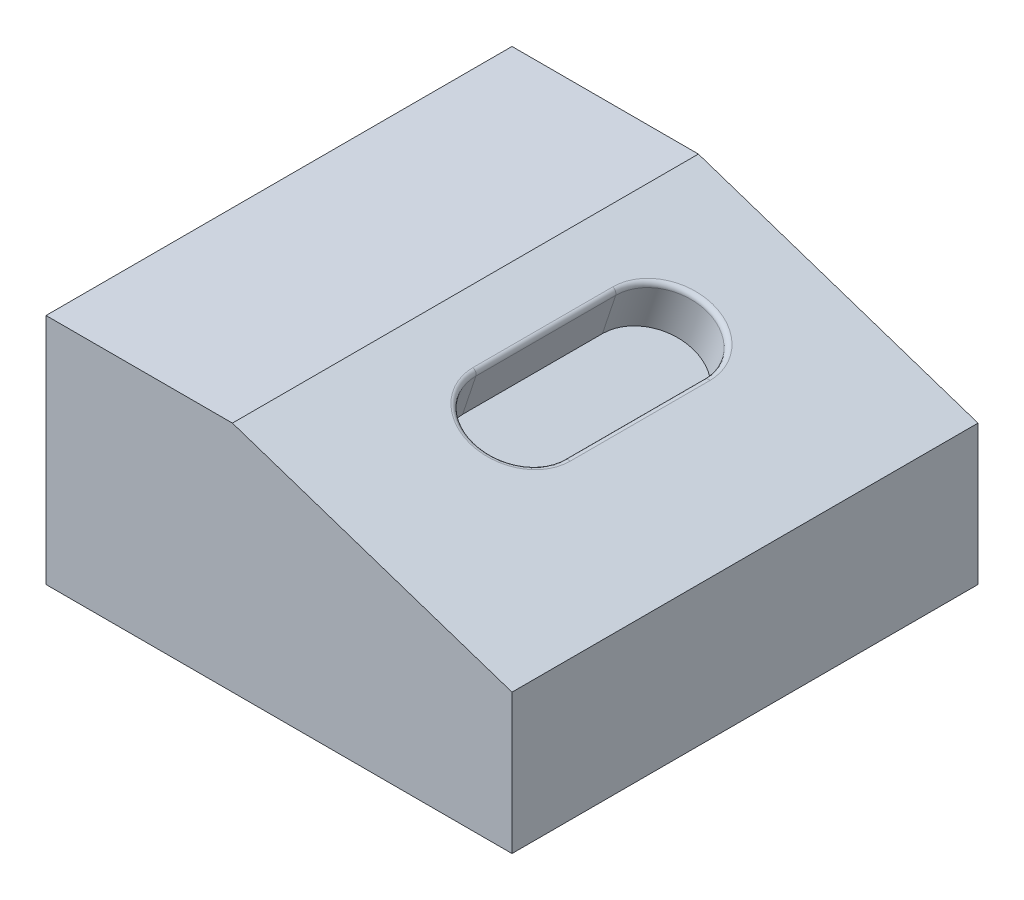
SolidWorks part; units mm, degrees
material "Ductile Iron"
ref_plane "Front Plane" through (0, 0, 0) normal (0, 0, 1) x (1, 0, 0)
ref_plane "Top Plane" through (0, 0, 0) normal (0, 1, 0) x (1, 0, 0)
ref_plane "Right Plane" through (0, 0, 0) normal (1, 0, 0) x (0, 0, -1)
sketch "Sketch1" plane through (0, 0, 0) normal (0, 0, 1) x (1, 0, 0)
  line L0 (0, 0) -> (0, 25)
  line L1 (0, 0) -> (50, 0)
  line L2 (0, 25) -> (20, 25)
  line L3 (20, 25) -> (50, 15)
  line L4 (50, 15) -> (50, 0)
  dimension "D1" = 25
  dimension "D2" = 50
  dimension "D3" = 20
  dimension "D4" = 15
extrude "Boss-Extrude2" add sketch "Sketch1" along normal blind 50
sketch "Sketch3" plane through (9.5, 28.5, 0) normal (0.3162, 0.9487, 0) x (0.9487, -0.3162, 0)
  line L0 (42.6907, 0) -> (11.068, 0) construction
  line L2 (17.6907, -15) -> (17.6907, -30)
  line L4 (27.6907, -15) -> (27.6907, -30)
  line L6 (42.6907, -50) -> (42.6907, 0) construction
  arc A0 (27.6907, -15) -> (17.6907, -15) centre (22.6907, -15) ccw
  arc A1 (17.6907, -30) -> (27.6907, -30) centre (22.6907, -30) ccw
  dimension "D1" = 15
  dimension "D2" = 10
  dimension "D3" = 15
  dimension "D4" = 15
extrude "Cut-Extrude2" cut sketch "Sketch3" against normal blind 5
fillet "Fillet1" radius 0.5 4 edges at (26.2829, 22.9057, 22.5) (31.0263, 21.3246, 10) (35.7698, 19.7434, 22.5) (31.0263, 21.3246, 35)
